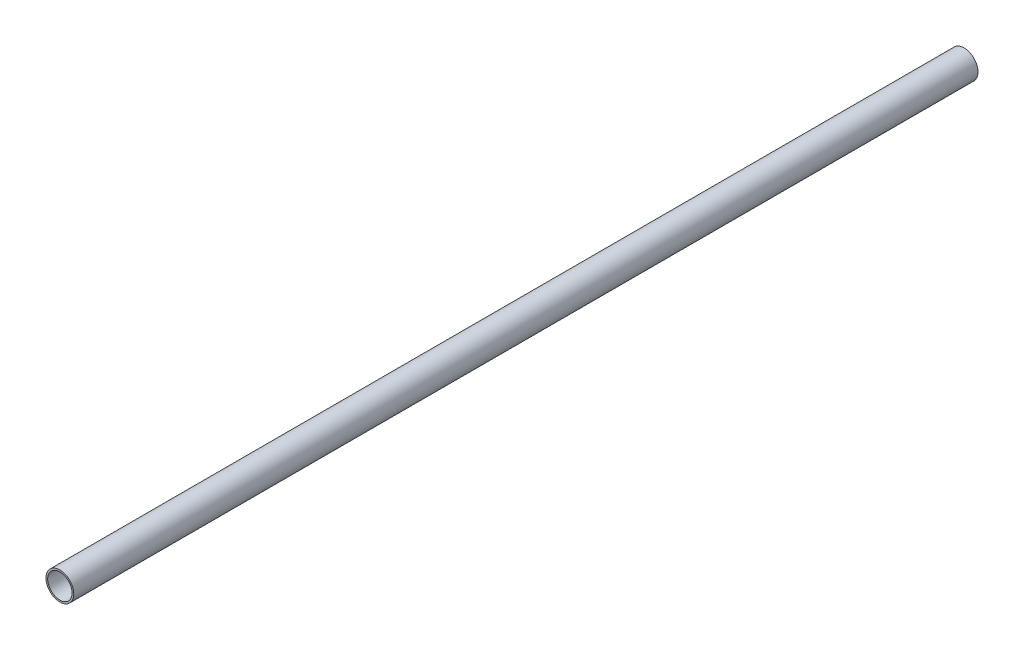
SolidWorks part; units mm, degrees
material "Thornel Mat VMA"
ref_plane "Front Plane" through (0, 0, 0) normal (0, 0, 1) x (1, 0, 0)
ref_plane "Top Plane" through (0, 0, 0) normal (0, 1, 0) x (1, 0, 0)
ref_plane "Right Plane" through (0, 0, 0) normal (1, 0, 0) x (0, 0, -1)
sketch "Sketch1" plane through (0, 0, 0) normal (0, 0, 1) x (1, 0, 0)
  circle A0 centre (0, 0) radius 7.239
  circle A1 centre (0, 0) radius 6.35
  dimension "D1" = 14.478
  dimension "D2" = 12.7
extrude "Boss-Extrude1" add sketch "Sketch1" along normal blind 470.8
